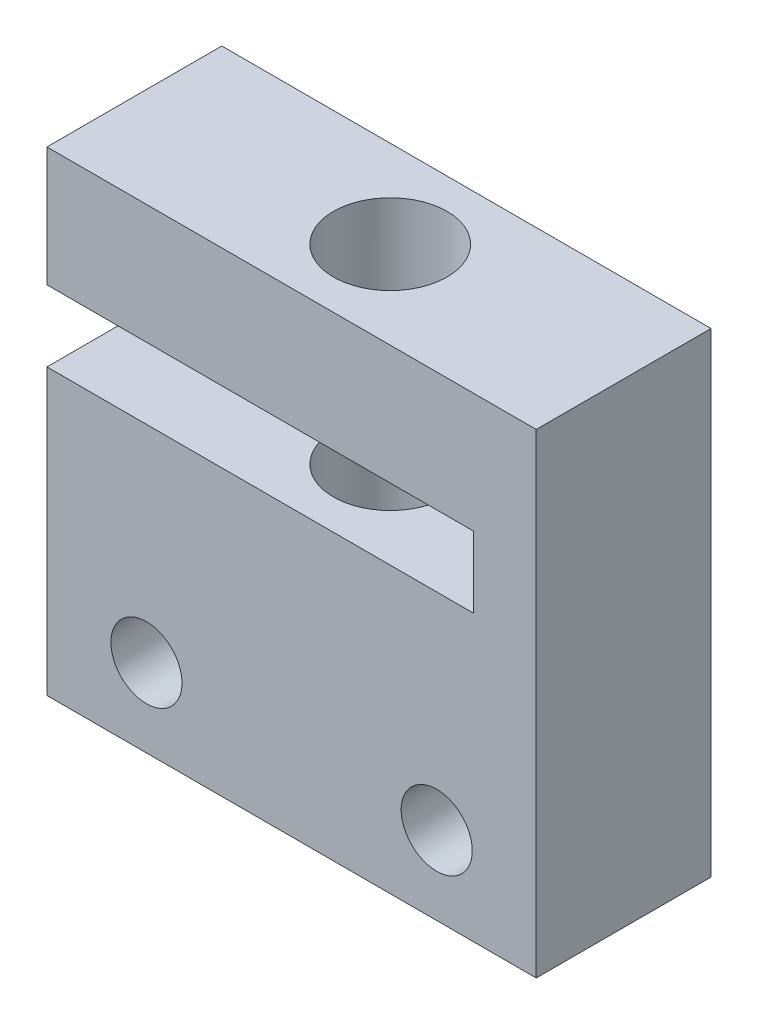
SolidWorks part; units mm, degrees
ref_plane "Front Plane" through (0, 0, 0) normal (0, 0, 1) x (1, 0, 0)
ref_plane "Top Plane" through (0, 0, 0) normal (0, 1, 0) x (1, 0, 0)
ref_plane "Right Plane" through (0, 0, 0) normal (1, 0, 0) x (0, 0, -1)
sketch "Sketch1" plane through (0, 0, 0) normal (0, 0, 1) x (1, 0, 0)
  line L0 (0, 25.02) -> (30, 25.02)
  line L1 (0, 33.42) -> (34.42, 33.42)
  line L2 (0, 33.42) -> (0, 25.02)
  line L3 (0, 0) -> (34.42, 0)
  line L4 (34.42, 33.42) -> (34.42, 0)
  line L5 (17.21, 0) -> (17.21, 20.02) construction
  line L7 (30, 25.02) -> (30, 20.02)
  line L8 (30, 20.02) -> (0, 20.02)
  line L9 (0, 20.02) -> (0, 0)
  circle A0 centre (27.42, 5.5) radius 2.5
  circle A2 centre (7, 5.5) radius 2.5
  point P0 (0, 0)
  dimension "D6" = 7
  dimension "D7" = 5.5
  dimension "D9" = 5
  dimension "D1" = 34.42
  dimension "D2" = 33.42
  dimension "D3" = 30
  dimension "D4" = 8.4
  dimension "D5" = 5
extrude "Boss-Extrude1" add sketch "Sketch1" along normal blind 12.3
sketch "Sketch2" plane through (0, 0, 0) normal (0, -1, 0) x (-1, 0, 0)
  line L0 (0, -12.3) -> (0, 0) construction
  circle A0 centre (-18, -6.15) radius 4
  point P4 (-18, -6.5639)
  point P5 (0, -6.15)
  dimension "D1" = 8
  dimension "D2" = 18
extrude "Cut-Extrude1" cut sketch "Sketch2" against normal through all
